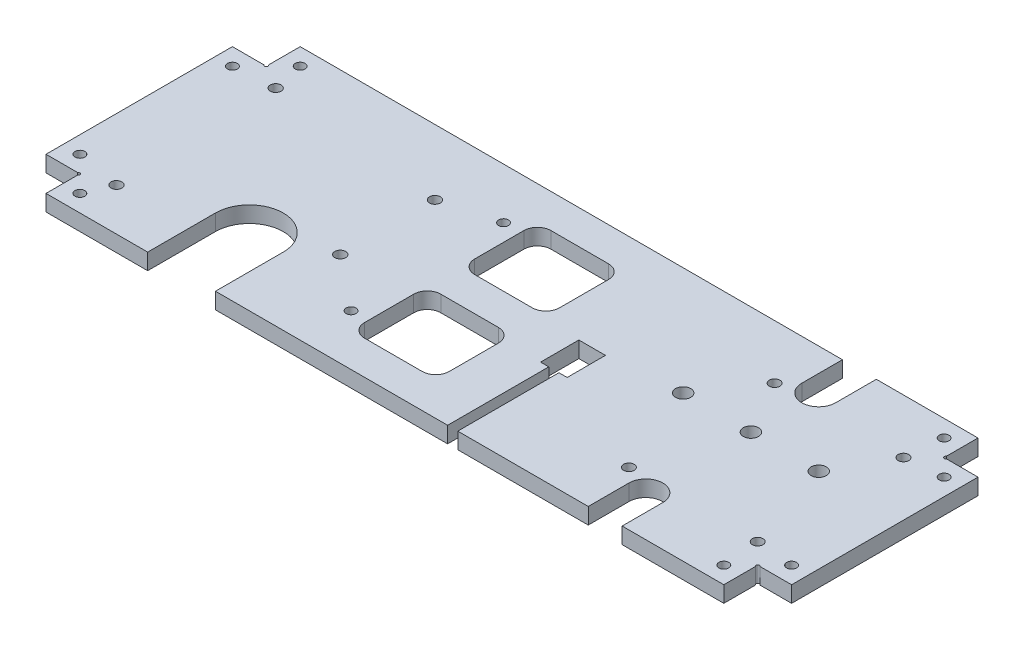
SolidWorks part; units mm, degrees
ref_plane "Front Plane" through (0, 0, 0) normal (0, 0, 1) x (1, 0, 0)
ref_plane "Top Plane" through (0, 0, 0) normal (0, 1, 0) x (1, 0, 0)
ref_plane "Right Plane" through (0, 0, 0) normal (1, 0, 0) x (0, 0, -1)
sketch "Sketch1" plane through (0, 0, 0) normal (0, 1, 0) x (1, 0, 0)
  line L0 (100, 37.5) -> (100, 27.5)
  line L1 (-100, 37.5) -> (100, 37.5)
  line L2 (-110, 27.5) -> (-110, -27.5)
  line L3 (-110, 0) -> (0, 0) construction
  line L4 (0, 37.5) -> (0, 0) construction
  line L5 (110, 27.5) -> (100, 27.5)
  line L6 (110, 27.5) -> (110, -27.5)
  line L7 (-110, 27.5) -> (-100, 27.5)
  line L8 (-100, 37.5) -> (-100, 27.5)
  line L9 (-110, -27.5) -> (-100, -27.5)
  line L10 (-100, -37.5) -> (-100, -27.5)
  line L11 (-100, -37.5) -> (100, -37.5)
  line L12 (100, -37.5) -> (100, -27.5)
  line L13 (110, -27.5) -> (100, -27.5)
  circle A0 centre (-95, 32.5) radius 1.45
  circle A1 centre (-105, 22.5) radius 1.45
  circle A2 centre (105, 22.5) radius 1.45
  circle A3 centre (95, 32.5) radius 1.45
  circle A4 centre (-105, -22.5) radius 1.45
  circle A5 centre (-95, -32.5) radius 1.45
  circle A6 centre (95, -32.5) radius 1.45
  circle A7 centre (105, -22.5) radius 1.45
  point P17 (110, 0)
  dimension "D4" = 2.9
  dimension "D1" = 37.5
  dimension "D2" = 110
  dimension "D3" = 10
  dimension "D5" = 32.5
  dimension "D6" = 22.5
  dimension "D7" = 95
  dimension "D8" = 105
extrude "Boss-Extrude1" add sketch "Sketch1" along normal blind 4.7625
sketch "Sketch2" plane through (0, 4.7625, 0) normal (0, 1, 0) x (1, 0, 0)
  line L0 (-105, -22.5) -> (-25, -22.5) construction
  line L1 (16.075, 3.65) -> (23.925, 3.65)
  line L2 (16.075, 3.65) -> (16.075, -7.65)
  line L3 (16.075, -7.65) -> (18.5, -7.65)
  line L4 (23.925, 3.65) -> (23.925, -7.65)
  line L5 (-25, 22.5) -> (-105, 22.5) construction
  line L6 (16.075, -2) -> (0, -2) construction
  line L7 (20, -37.5) -> (20, 3.65) construction
  line L8 (-110, 27.5) -> (-110, -27.5) construction
  line L9 (-107, 25.84) -> (-107, -27.5) construction
  line L10 (-107, -27.5) -> (-58.067, -27.5) construction
  line L11 (-107, 25.84) -> (-63.3908, 25.84) construction
  line L15 (-100, -37.5) -> (100, -37.5) construction
  line L16 (-100, -37.5) -> (100, -37.5) construction
  line L17 (45, 5.5) -> (65, 5.5) construction
  line L18 (65, 5.5) -> (85, 5.5) construction
  line L19 (65, 37.5) -> (65, 25.5) construction
  line L20 (100, 37.5) -> (-100, 37.5) construction
  line L21 (70, 37.5) -> (70, 25.5)
  line L22 (60, 37.5) -> (60, 25.5)
  line L23 (65, -37.5) -> (65, -25.5) construction
  line L24 (60, -37.5) -> (60, -25.5)
  line L25 (70, -37.5) -> (70, -25.5)
  line L26 (21.5, -7.65) -> (23.925, -7.65)
  line L27 (21.5, -37.5) -> (18.5, -37.5)
  line L28 (21.5, -37.5) -> (21.5, -7.65)
  line L29 (56, 0) -> (0, 0) construction
  line L30 (18.5, -37.5) -> (18.5, -7.65)
  line L31 (56, -21.5) -> (94, -21.5) construction
  line L32 (56, -21.5) -> (56, 21.5) construction
  line L33 (56, 21.5) -> (94, 21.5) construction
  line L34 (94, -21.5) -> (94, 21.5) construction
  line L35 (75, -21.5) -> (75, 21.5) construction
  line L36 (-100, 27.5) -> (-110, 27.5) construction
  line L37 (-20, -27.5) -> (5, -27.5)
  line L38 (-20, -27.5) -> (-20, -5)
  line L39 (-20, -5) -> (5, -5)
  line L40 (5, -27.5) -> (5, -5)
  line L41 (-20, 27.5) -> (5, 27.5)
  line L42 (-20, 27.5) -> (-20, 5)
  line L43 (-20, 5) -> (5, 5)
  line L44 (5, 27.5) -> (5, 5)
  line L45 (-110, -27.5) -> (-100, -27.5) construction
  line L46 (-60, -37.5) -> (-60, -17.5) construction
  line L47 (-70, -37.5) -> (-70, -17.5)
  line L48 (-50, -37.5) -> (-50, -17.5)
  circle A0 centre (-25, -22.5) radius 1.45
  circle A1 centre (-25, 22.5) radius 1.45
  circle A2 centre (-105, -22.5) radius 1.45 construction
  circle A3 centre (-91.76, -24.96) radius 1.6
  circle A4 centre (-93.03, 23.3) radius 1.6
  circle A5 centre (-40.96, -9.72) radius 1.6
  circle A6 centre (-40.96, 18.22) radius 1.6
  circle A7 centre (45, 5.5) radius 2.25
  circle A8 centre (65, 5.5) radius 2.25
  circle A9 centre (85, 5.5) radius 2.25
  arc A10 (70, 37.5) -> (60, 37.5) centre (65, 37.5) ccw
  arc A11 (60, 25.5) -> (70, 25.5) centre (65, 25.5) ccw
  arc A12 (60, -37.5) -> (70, -37.5) centre (65, -37.5) ccw
  arc A13 (70, -25.5) -> (60, -25.5) centre (65, -25.5) ccw
  circle A14 centre (56, -21.5) radius 1.5625
  circle A15 centre (94, -21.5) radius 1.5625
  circle A16 centre (94, 21.5) radius 1.5625
  circle A17 centre (56, 21.5) radius 1.5625
  arc A18 (-70, -37.5) -> (-50, -37.5) centre (-60, -37.5) ccw
  arc A19 (-50, -17.5) -> (-70, -17.5) centre (-60, -17.5) ccw
  point P49 (65, 31.5)
  point P54 (65, -31.5)
  point P91 (-60, -27.5)
  dimension "D10" = 3.2
  dimension "D17" = 4.5
  dimension "D25" = 3.125
  dimension "D1" = 7.85
  dimension "D2" = 11.3
  dimension "D3" = 20
  dimension "D4" = 85
  dimension "D5" = 3
  dimension "D6" = 53.34
  dimension "D7" = 10
  dimension "D8" = 15.24
  dimension "D9" = 50.8
  dimension "D11" = 2.54
  dimension "D12" = 13.97
  dimension "D13" = 7.62
  dimension "D14" = 27.94
  dimension "D15" = 50.8
  dimension "D16" = 43
  dimension "D18" = 20
  dimension "D19" = 65
  dimension "D20" = 2
  dimension "D21" = 10
  dimension "D22" = 12
  dimension "D23" = 10
  dimension "D24" = 3
  dimension "D26" = 38
  dimension "D27" = 43
  dimension "D28" = 75
  dimension "D29" = 5
  dimension "D30" = 10
  dimension "D31" = 25
  dimension "D32" = 20
  dimension "D33" = 20
  dimension "D34" = 60
extrude "Cut-Extrude1" cut sketch "Sketch2" against normal through all
sketch "Sketch3" plane through (0, 4.7625, 0) normal (0, 1, 0) x (1, 0, 0)
  line L0 (100.25, 27.75) -> (100, 27.75) construction
  line L1 (100, 27.5) -> (100, 37.5) construction
  line L2 (100.25, 27.75) -> (100.25, 27.5) construction
  line L3 (110, 27.5) -> (100, 27.5) construction
  line L4 (100.25, -27.75) -> (100.25, -27.5) construction
  line L5 (100, -27.5) -> (110, -27.5) construction
  line L6 (100.25, -27.75) -> (100, -27.75) construction
  line L7 (100, -37.5) -> (100, -27.5) construction
  line L8 (-100.25, -27.75) -> (-100, -27.75) construction
  line L9 (-100, -27.5) -> (-100, -37.5) construction
  line L10 (-100.25, -27.75) -> (-100.25, -27.5) construction
  line L11 (-110, -27.5) -> (-100, -27.5) construction
  line L12 (-100.25, 27.75) -> (-100, 27.75) construction
  line L13 (-100, 37.5) -> (-100, 27.5) construction
  line L14 (-100.25, 27.75) -> (-100.25, 27.5) construction
  line L15 (-100, 27.5) -> (-110, 27.5) construction
  circle A0 centre (-100.25, 27.75) radius 0.5
  circle A1 centre (-100.25, -27.75) radius 0.5
  circle A2 centre (100.25, -27.75) radius 0.5
  circle A3 centre (100.25, 27.75) radius 0.5
  dimension "D2" = 1
  dimension "D1" = 0.25
extrude "Cut-Extrude2" cut sketch "Sketch3" against normal through all
fillet "Fillet1" radius 4 8 edges at (-20, 2.3813, -27.5) (-20, 2.3813, 5) (5, 2.3813, 5) (5, 2.3813, -27.5) (5, 2.3813, -5) (5, 2.3813, 27.5) (-20, 2.3813, 27.5) (-20, 2.3813, -5)
